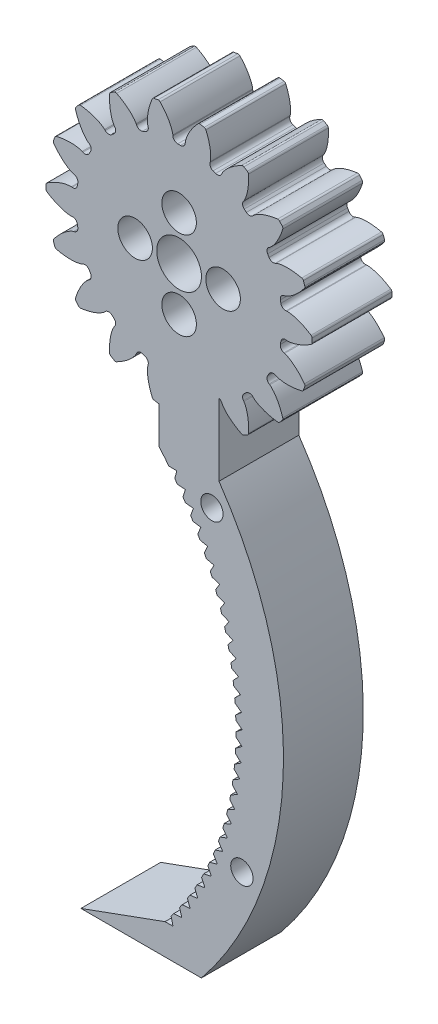
SolidWorks part; units mm, degrees
material "Alloy Steel"
ref_plane "Front" through (0, 0, 0) normal (0, 0, 1) x (1, 0, 0)
ref_plane "Top" through (0, 0, 0) normal (0, 1, 0) x (1, 0, 0)
ref_plane "Right" through (0, 0, 0) normal (1, 0, 0) x (0, 0, -1)
sketch "Sketch1" plane through (0, 0, 0) normal (0, 0, 1) x (1, 0, 0)
  circle A0 centre (0, 0) radius 21.1667
extrude "Boss-Extrude1" add sketch "Sketch1" along normal blind 12.7
sketch "Sketch3" plane through (0, 0, 0) normal (0, 0, 1) x (1, 0, 0)
  line L0 (0, 0) -> (43.7181, 0) construction
  line L2 (0, 0) -> (-0.9393, 16.3773) construction
  line L3 (0, 0) -> (0.9393, 16.3773) construction
  line L4 (0.9393, 16.3773) -> (0.9886, 17.2368) construction
  line L5 (0, 0) -> (0, 61.276) construction
  line L6 (-0.9393, 16.3773) -> (-0.9886, 17.2368) construction
  circle A0 centre (0, 0) radius 21.1667 construction
  circle A1 centre (0, 0) radius 19.05 construction
  circle A2 centre (0, 0) radius 17.2652 construction
  arc A3 (0.9393, 16.3773) -> (-0.9393, 16.3773) centre (0, 0) ccw construction
  arc A5 (3.1554, 20.9302) -> (-3.1554, 20.9302) centre (0, 0) ccw
  spline S0 degree 4 poles (-0.9886, 17.2368) (-0.9891, 17.2432) (-0.9907, 17.2612) (-0.9949, 17.295) (-1.0034, 17.35) (-1.0167, 17.4198) (-1.0366, 17.5096) (-1.0637, 17.6148) (-1.0972, 17.7297) (-1.1377, 17.8539) (-1.1816, 17.977) (-1.2287, 18.099) (-1.2785, 18.2198) (-1.3423, 18.3651) (-1.4236, 18.5381) (-1.5256, 18.738) (-1.6493, 18.9622) (-1.784, 19.1875) (-1.9235, 19.4067) (-2.0724, 19.6249) (-2.2221, 19.8338) (-2.3856, 20.0472) (-2.5406, 20.2425) (-2.7229, 20.4571) (-2.8726, 20.6291) (-3.0791, 20.8514) (-3.2038, 20.9813) (-3.3529, 21.1316) (-3.4207, 21.1975) (-3.4624, 21.2381) knots 0 0 0 0 0 0.005377 0.015084 0.028532 0.04661 0.064855 0.092111 0.119476 0.146842 0.174209 0.201575 0.228941 0.256307 0.307035 0.361767 0.4165 0.471232 0.525964 0.580697 0.635429 0.690161 0.744894 0.799626 0.854358 0.909091 0.954545 1 1 1 1 1 construction
  spline S1 degree 4 poles (-0.9886, 17.2368) (-0.9891, 17.2432) (-0.9907, 17.2612) (-0.9949, 17.295) (-1.0034, 17.35) (-1.0167, 17.4198) (-1.0366, 17.5096) (-1.0637, 17.6148) (-1.0972, 17.7297) (-1.1377, 17.8539) (-1.1816, 17.977) (-1.2287, 18.099) (-1.2785, 18.2198) (-1.3423, 18.3651) (-1.4236, 18.5381) (-1.5256, 18.738) (-1.6493, 18.9622) (-1.784, 19.1875) (-1.9235, 19.4067) (-2.0724, 19.6249) (-2.2221, 19.8338) (-2.3856, 20.0472) (-2.5406, 20.2425) (-2.7229, 20.4571) (-2.8726, 20.6291) (-3.0344, 20.8032) (-3.1141, 20.8874) (-3.1554, 20.9302) knots 0 0 0 0 0 0.005377 0.015084 0.028532 0.04661 0.064855 0.092111 0.119476 0.146842 0.174209 0.201575 0.228941 0.256307 0.307035 0.361767 0.4165 0.471232 0.525964 0.580697 0.635429 0.690161 0.744894 0.799626 0.854358 0.909091 0.909091 0.909091 0.909091 0.909091
  spline S2 degree 4 poles (0.9886, 17.2368) (0.9891, 17.2432) (0.9907, 17.2612) (0.9949, 17.295) (1.0034, 17.35) (1.0167, 17.4198) (1.0366, 17.5096) (1.0637, 17.6148) (1.0972, 17.7297) (1.1377, 17.8539) (1.1816, 17.977) (1.2287, 18.099) (1.2785, 18.2198) (1.3423, 18.3651) (1.4236, 18.5381) (1.5256, 18.738) (1.6493, 18.9622) (1.784, 19.1875) (1.9235, 19.4067) (2.0724, 19.6249) (2.2221, 19.8338) (2.3856, 20.0472) (2.5406, 20.2425) (2.7229, 20.4571) (2.8726, 20.6291) (3.0791, 20.8514) (3.2038, 20.9813) (3.3529, 21.1316) (3.4207, 21.1975) (3.4624, 21.2381) knots 0 0 0 0 0 0.005377 0.015084 0.028532 0.04661 0.064855 0.092111 0.119476 0.146842 0.174209 0.201575 0.228941 0.256307 0.307035 0.361767 0.4165 0.471232 0.525964 0.580697 0.635429 0.690161 0.744894 0.799626 0.854358 0.909091 0.954545 1 1 1 1 1 construction
  spline S3 degree 4 poles (0.9886, 17.2368) (0.9891, 17.2432) (0.9907, 17.2612) (0.9949, 17.295) (1.0034, 17.35) (1.0167, 17.4198) (1.0366, 17.5096) (1.0637, 17.6148) (1.0972, 17.7297) (1.1377, 17.8539) (1.1816, 17.977) (1.2287, 18.099) (1.2785, 18.2198) (1.3423, 18.3651) (1.4236, 18.5381) (1.5256, 18.738) (1.6493, 18.9622) (1.784, 19.1875) (1.9235, 19.4067) (2.0724, 19.6249) (2.2221, 19.8338) (2.3856, 20.0472) (2.5406, 20.2425) (2.7229, 20.4571) (2.8726, 20.6291) (3.0344, 20.8032) (3.1141, 20.8874) (3.1554, 20.9302) knots 0 0 0 0 0 0.005377 0.015084 0.028532 0.04661 0.064855 0.092111 0.119476 0.146842 0.174209 0.201575 0.228941 0.256307 0.307035 0.361767 0.4165 0.471232 0.525964 0.580697 0.635429 0.690161 0.744894 0.799626 0.854358 0.909091 0.909091 0.909091 0.909091 0.909091
  point P0 (0, 16.4042)
sketch "DCLTBC" plane through (0, 0, 0) normal (0, 0, 1) x (1, 0, 0)
  line L0 (0, 0) -> (41.04, 0) construction
  line L1 (-0.9393, 16.3773) -> (-0.9886, 17.2368) construction
  line L2 (0.9393, 16.3773) -> (0.9886, 17.2368) construction
  line L3 (-0.9393, 16.3773) -> (-0.9886, 17.2368)
  line L4 (0.9393, 16.3773) -> (0.9886, 17.2368)
  line L5 (0, 0) -> (0, 104.9356) construction
  circle A0 centre (0, 0) radius 21.1667
  circle A1 centre (0, 0) radius 19.05 construction
  circle A2 centre (0, 0) radius 17.2652 construction
  arc A3 (0.9393, 16.3773) -> (-0.9393, 16.3773) centre (0, 0) ccw construction
  arc A4 (0.9393, 16.3773) -> (-0.9393, 16.3773) centre (0, 0) ccw
  spline S0 degree 4 poles (-998.2859, -55.9585) (-15.2714, 14.5763) (-1.1564, 16.0258) (-0.9033, 16.703) (-1.0034, 17.35) (-1.0167, 17.4198) (-1.0366, 17.5096) (-1.0637, 17.6148) (-1.0972, 17.7297) (-1.1377, 17.8539) (-1.1816, 17.977) (-1.2287, 18.099) (-1.2785, 18.2198) (-1.3423, 18.3651) (-1.4236, 18.5381) (-1.5256, 18.738) (-1.6493, 18.9622) (-1.784, 19.1875) (-1.9235, 19.4067) (-2.0724, 19.6249) (-2.2221, 19.8338) (-2.3856, 20.0472) (-2.5406, 20.2425) (-2.7229, 20.4571) (-3.4042, 21.2399) (-5.6764, 23.4628) (17.3745, -0.7418) (-697.1444, 740.8893) knots -0.501613 -0.501613 -0.501613 -0.501613 -0.501613 0.005377 0.015084 0.028532 0.04661 0.064855 0.092111 0.119476 0.146842 0.174209 0.201575 0.228941 0.256307 0.307035 0.361767 0.4165 0.471232 0.525964 0.580697 0.635429 0.690161 0.744894 0.799626 0.854358 1.68661 1.68661 1.68661 1.68661 1.68661 only from (-0.9886, 17.2368) to (-3.1554, 20.9302) construction
  spline S1 degree 4 poles (998.2859, -55.9585) (15.2714, 14.5763) (1.1564, 16.0258) (0.9033, 16.703) (1.0034, 17.35) (1.0167, 17.4198) (1.0366, 17.5096) (1.0637, 17.6148) (1.0972, 17.7297) (1.1377, 17.8539) (1.1816, 17.977) (1.2287, 18.099) (1.2785, 18.2198) (1.3423, 18.3651) (1.4236, 18.5381) (1.5256, 18.738) (1.6493, 18.9622) (1.784, 19.1875) (1.9235, 19.4067) (2.0724, 19.6249) (2.2221, 19.8338) (2.3856, 20.0472) (2.5406, 20.2425) (2.7229, 20.4571) (3.4042, 21.2399) (5.6764, 23.4628) (-17.3745, -0.7418) (697.1444, 740.8893) knots -0.501613 -0.501613 -0.501613 -0.501613 -0.501613 0.005377 0.015084 0.028532 0.04661 0.064855 0.092111 0.119476 0.146842 0.174209 0.201575 0.228941 0.256307 0.307035 0.361767 0.4165 0.471232 0.525964 0.580697 0.635429 0.690161 0.744894 0.799626 0.854358 1.68661 1.68661 1.68661 1.68661 1.68661 only from (0.9886, 17.2368) to (3.1554, 20.9302) construction
  spline S2 degree 4 poles (-0.9886, 17.2368) (-0.9891, 17.2432) (-0.9907, 17.2612) (-0.9949, 17.295) (-1.0034, 17.35) (-1.0167, 17.4198) (-1.0366, 17.5096) (-1.0637, 17.6148) (-1.0972, 17.7297) (-1.1377, 17.8539) (-1.1816, 17.977) (-1.2287, 18.099) (-1.2785, 18.2198) (-1.3423, 18.3651) (-1.4236, 18.5381) (-1.5256, 18.738) (-1.6493, 18.9622) (-1.784, 19.1875) (-1.9235, 19.4067) (-2.0724, 19.6249) (-2.2221, 19.8338) (-2.3856, 20.0472) (-2.5406, 20.2425) (-2.7229, 20.4571) (-2.8726, 20.6291) (-3.0344, 20.8032) (-3.1141, 20.8874) (-3.1554, 20.9302) knots 0 0 0 0 0 0.005377 0.015084 0.028532 0.04661 0.064855 0.092111 0.119476 0.146842 0.174209 0.201575 0.228941 0.256307 0.307035 0.361767 0.4165 0.471232 0.525964 0.580697 0.635429 0.690161 0.744894 0.799626 0.854358 0.909091 0.909091 0.909091 0.909091 0.909091
  spline S3 degree 4 poles (0.9886, 17.2368) (0.9891, 17.2432) (0.9907, 17.2612) (0.9949, 17.295) (1.0034, 17.35) (1.0167, 17.4198) (1.0366, 17.5096) (1.0637, 17.6148) (1.0972, 17.7297) (1.1377, 17.8539) (1.1816, 17.977) (1.2287, 18.099) (1.2785, 18.2198) (1.3423, 18.3651) (1.4236, 18.5381) (1.5256, 18.738) (1.6493, 18.9622) (1.784, 19.1875) (1.9235, 19.4067) (2.0724, 19.6249) (2.2221, 19.8338) (2.3856, 20.0472) (2.5406, 20.2425) (2.7229, 20.4571) (2.8726, 20.6291) (3.0344, 20.8032) (3.1141, 20.8874) (3.1554, 20.9302) knots 0 0 0 0 0 0.005377 0.015084 0.028532 0.04661 0.064855 0.092111 0.119476 0.146842 0.174209 0.201575 0.228941 0.256307 0.307035 0.361767 0.4165 0.471232 0.525964 0.580697 0.635429 0.690161 0.744894 0.799626 0.854358 0.909091 0.909091 0.909091 0.909091 0.909091
extrude "Cut-Extrude-DCLTBC" cut sketch "DCLTBC" along normal through all
fillet "Fillet-Tip-DCLTBC" radius 0.3764 2 edges at (3.1554, 20.9302, 6.35) (-3.1554, 20.9302, 6.35)
fillet "Fillet-Root-DCLTBC" radius 0.7528 2 edges at (-0.9393, 16.3773, 6.35) (0.9393, 16.3773, 6.35)
pattern_circular "CirPattern-DCLTBC" count 18 over 360 about axis through (0, 0, 12.7) along (0, 0, 1) of "Cut-Extrude-DCLTBC", "Fillet-Tip-DCLTBC", "Fillet-Root-DCLTBC"
sketch "DCGTBC" [suppressed] plane through (0, 0, 0) normal (0, 0, 1) x (1, 0, 0)
  line L0 (0, 0) -> (41.04, 0) construction
  line L1 (-22.6634, 1.9828) -> (0, 0) construction
  line L2 (0, 0) -> (22.6634, 1.9828) construction
  line L3 (0, 0) -> (-16.5124, 0)
  line L5 (0, 0) -> (0, 104.9356) construction
  circle A0 centre (0, 0) radius 25
  circle A1 centre (0, 0) radius 24 construction
  circle A2 centre (0, 0) radius 21.7514 construction
  arc A3 (0.0626, 22.7499) -> (-0.0626, 22.7499) centre (0, 0) ccw construction
  arc A11 (22.6634, 1.9828) -> (-22.6634, 1.9828) centre (0, 0) ccw
  spline S4 degree 4 poles (999.7589, -2.0808) (12.8658, 20.0937) (0.2547, 20.6746) (0.0189, 21.2606) (0.0654, 21.8429) (0.0715, 21.8997) (0.0812, 21.973) (0.095, 22.0592) (0.1126, 22.1539) (0.1343, 22.2566) (0.1583, 22.3589) (0.1845, 22.4607) (0.2124, 22.562) (0.2486, 22.6844) (0.2952, 22.8308) (0.3543, 23.0013) (0.4268, 23.1939) (0.5065, 23.3893) (0.5897, 23.5809) (0.6793, 23.7735) (0.7698, 23.9592) (0.8695, 24.151) (0.9643, 24.3275) (1.0767, 24.524) (1.517, 25.277) (3.0654, 27.5692) (-13.787, 0.9944) (540.7091, 867.0187) knots -0.561807 -0.561807 -0.561807 -0.561807 -0.561807 0.005377 0.015084 0.028532 0.04661 0.064855 0.092111 0.119476 0.146842 0.174209 0.201575 0.228941 0.256307 0.307035 0.361767 0.4165 0.471232 0.525964 0.580697 0.635429 0.690161 0.744894 0.799626 0.854358 1.731906 1.731906 1.731906 1.731906 1.731906 only from (0.0598, 21.7513) to (1.3455, 24.9638) construction
  spline S5 degree 4 poles (-999.7589, -2.0808) (-12.8658, 20.0937) (-0.2547, 20.6746) (-0.0189, 21.2606) (-0.0654, 21.8429) (-0.0715, 21.8997) (-0.0812, 21.973) (-0.095, 22.0592) (-0.1126, 22.1539) (-0.1343, 22.2566) (-0.1583, 22.3589) (-0.1845, 22.4607) (-0.2124, 22.562) (-0.2486, 22.6844) (-0.2952, 22.8308) (-0.3543, 23.0013) (-0.4268, 23.1939) (-0.5065, 23.3893) (-0.5897, 23.5809) (-0.6793, 23.7735) (-0.7698, 23.9592) (-0.8695, 24.151) (-0.9643, 24.3275) (-1.0767, 24.524) (-1.517, 25.277) (-3.0654, 27.5692) (13.787, 0.9944) (-540.7091, 867.0187) knots -0.561807 -0.561807 -0.561807 -0.561807 -0.561807 0.005377 0.015084 0.028532 0.04661 0.064855 0.092111 0.119476 0.146842 0.174209 0.201575 0.228941 0.256307 0.307035 0.361767 0.4165 0.471232 0.525964 0.580697 0.635429 0.690161 0.744894 0.799626 0.854358 1.731906 1.731906 1.731906 1.731906 1.731906 only from (-0.0598, 21.7513) to (-1.3455, 24.9638) construction
  spline S6 degree 4 poles (0.0598, 21.7513) (0.0599, 21.7565) (0.0603, 21.7709) (0.0618, 21.7983) (0.0654, 21.8429) (0.0715, 21.8997) (0.0812, 21.973) (0.095, 22.0592) (0.1126, 22.1539) (0.1343, 22.2566) (0.1583, 22.3589) (0.1845, 22.4607) (0.2124, 22.562) (0.2486, 22.6844) (0.2952, 22.8308) (0.3543, 23.0013) (0.4268, 23.1939) (0.5065, 23.3893) (0.5897, 23.5809) (0.6793, 23.7735) (0.7698, 23.9592) (0.8695, 24.151) (0.9643, 24.3275) (1.0767, 24.524) (1.1693, 24.6823) (1.27, 24.8447) (1.3197, 24.9235) (1.3455, 24.9638) knots 0 0 0 0 0 0.005377 0.015084 0.028532 0.04661 0.064855 0.092111 0.119476 0.146842 0.174209 0.201575 0.228941 0.256307 0.307035 0.361767 0.4165 0.471232 0.525964 0.580697 0.635429 0.690161 0.744894 0.799626 0.854358 0.909091 0.909091 0.909091 0.909091 0.909091
  spline S7 degree 4 poles (-0.0598, 21.7513) (-0.0599, 21.7565) (-0.0603, 21.7709) (-0.0618, 21.7983) (-0.0654, 21.8429) (-0.0715, 21.8997) (-0.0812, 21.973) (-0.095, 22.0592) (-0.1126, 22.1539) (-0.1343, 22.2566) (-0.1583, 22.3589) (-0.1845, 22.4607) (-0.2124, 22.562) (-0.2486, 22.6844) (-0.2952, 22.8308) (-0.3543, 23.0013) (-0.4268, 23.1939) (-0.5065, 23.3893) (-0.5897, 23.5809) (-0.6793, 23.7735) (-0.7698, 23.9592) (-0.8695, 24.151) (-0.9643, 24.3275) (-1.0767, 24.524) (-1.1693, 24.6823) (-1.27, 24.8447) (-1.3197, 24.9235) (-1.3455, 24.9638) knots 0 0 0 0 0 0.005377 0.015084 0.028532 0.04661 0.064855 0.092111 0.119476 0.146842 0.174209 0.201575 0.228941 0.256307 0.307035 0.361767 0.4165 0.471232 0.525964 0.580697 0.635429 0.690161 0.744894 0.799626 0.854358 0.909091 0.909091 0.909091 0.909091 0.909091
  dimension "D1" = 5
  dimension "D2" = 5
extrude "Cut-Extrude-DCGTBC" [suppressed] cut sketch "DCGTBC" along normal through all
fillet "Fillet-Tip-DCGTBC" [suppressed] radius 0.3764
pattern_circular "CirPattern-DCGTBC" [suppressed] count 18 over 360
sketch "Sketch4" plane through (0, 0, 12.7) normal (0, 0, 1) x (1, 0, 0)
  circle A1 centre (0, 0) radius 3.556
  dimension "D1" = 7.112
extrude "Cut-Extrude2" cut sketch "Sketch4" against normal through all
sketch "Sketch5" plane through (0, 0, 12.7) normal (0, 0, 1) x (1, 0, 0)
  circle A0 centre (-7, 0) radius 1
  circle A1 centre (0, 7) radius 1
  circle A2 centre (7, 0) radius 1
  circle A3 centre (0, -7) radius 1
  point P12 (0, 0)
  dimension "D2" = 2
  dimension "D1" = 7
  dimension "D3" = 4
extrude "Cut-Extrude3" cut sketch "Sketch5" against normal through all
sketch "Sketch7" plane through (0, 0, 12.7) normal (0, 0, 1) x (1, 0, 0)
  line L0 (6.35, -14.1137) -> (6.35, -26.8137)
  line L2 (-3.175, -26.8137) -> (-3.175, -14.1137)
  line L3 (-3.175, -14.1137) -> (6.35, -14.1137)
  line L4 (-2.2365, -91.7884) -> (-15.6293, -96.6637)
  line L5 (-15.6293, -96.6637) -> (3.5477, -96.6637)
  arc A0 (-3.175, -26.8137) -> (-2.2365, -91.7884) centre (-41.7528, -59.8651) cw
  arc A1 (6.35, -26.8137) -> (3.5477, -96.6637) centre (-41.7528, -59.8651) cw
  dimension "D3" = 50.8
  dimension "D1" = 9.525
  dimension "D2" = 12.7
  dimension "D4" = 82.55
  dimension "D5" = 3.175
  dimension "D6" = 77.6747
  dimension "D7" = 19.177
extrude "Boss-Extrude3" add sketch "Sketch7" against normal through all
sketch "Sketch9" plane through (0, 0, 12.7) normal (0, 0, 1) x (1, 0, 0)
  circle A0 centre (5.2228, -31.0331) radius 1.778
  arc A1 (3.5477, -96.6637) -> (6.35, -26.8137) centre (-41.7528, -59.8651) ccw construction
  circle A2 centre (9.9936, -78.8467) radius 1.778
  arc A3 (-2.2365, -91.7884) -> (-3.175, -26.8137) centre (-41.7528, -59.8651) ccw construction
  dimension "D1" = 3.556
  dimension "D2" = 55.118
  dimension "D3" = 3.556
  dimension "D4" = 55.118
extrude "Cut-Extrude4" cut sketch "Sketch9" against normal blind 101.6
sketch "Sketch10" plane through (0, 0, 12.7) normal (0, 0, 1) x (1, 0, 0)
  circle A0 centre (-7, 0) radius 2.75
  circle A1 centre (0, -7) radius 2.75
  circle A2 centre (7, 0) radius 2.75
  circle A3 centre (0, 7) radius 2.75
  dimension "D1" = 5.5
extrude "Cut-Extrude5" cut sketch "Sketch10" against normal blind 7.7
sketch "Sketch11" plane through (0, 0, 12.7) normal (0, 0, 1) x (1, 0, 0)
  line L0 (-2.2365, -91.7884) -> (-0.9665, -91.7884)
  line L1 (-0.9665, -91.7884) -> (-1.2716, -90.5556)
  arc A0 (-2.2365, -91.7884) -> (-3.175, -26.8137) centre (-41.7528, -59.8651) ccw construction
  arc A1 (-2.2365, -91.7884) -> (-1.2716, -90.5556) centre (-41.7528, -59.8651) ccw
  dimension "D1" = 1.27
  dimension "D2" = 1.27
extrude "Cut-Extrude6" cut sketch "Sketch11" against normal through all
pattern_circular "CirPattern1" count 30 over 75 about axis through (-41.7528, -59.8651, 0) along (0, 0, 1) of "Cut-Extrude6"
equation "\"DiametralPitch\"= 12'Diametral Pitch"
equation "\"NumTeeth\"= 18'Number of Teeth"
equation "\"PressureAngle\"= 25deg'Pressure Angle"
equation "\"Addendum\"= 1 / \"DiametralPitch\"'Addendum"
equation "\"Dedendum\"= 1.25 / \"DiametralPitch\"'Dedendum"
equation "\"WorkingDepth\"= 2 / \"DiametralPitch\"'Working Depth - here for REF (Not used in building model)"
equation "\"WholeDepth\"= 2.25 / \"DiametralPitch\"'Whole Depth - here for REF (Not used in building model)"
equation "\"Clearance\"= .25 / \"DiametralPitch\"'Clearance"
equation "\"CircularPitch\"= pi / \"DiametralPitch\"'Circular Pitch - here for REF (Not used in building model)"
equation "\"PitchCircle\"= \"NumTeeth\" / \"DiametralPitch\"'Pitch Circle - or - Pitch Diameter"
equation "\"OutsideDiameter\"= ( \"NumTeeth\" + 2 ) / \"DiametralPitch\"'Outside Diameter"
equation "\"Fillet_Root\"= \"Clearance\" * cos ( \"PressureAngle\" ) * tan ( ( 90 + \"PressureAngle\" ) / 2 ) 'Fillet Root"
equation "\"AddendumCircle\"= \"PitchCircle\" + ( 2 * \"Addendum\" )'Addendum Circle - or - Addendum Diameter"
equation "\"DedendumCircle\"= \"PitchCircle\" - ( 2 * \"Dedendum\" )'Dedendum Circle - or - Dedendum Diameter"
equation "\"BaseCircle\"= \"PitchCircle\" * cos ( \"PressureAngle\" )'Base Circle - Base Diameter"
equation "\"PitchAngle\"= 360deg / \"NumTeeth\"'Pitch Angle"
equation "\"Alpha\"= sqr ( \"PitchCircle\" ^ 2 - \"BaseCircle\" ^ 2 ) / \"BaseCircle\" * 180 / PI - \"PressureAngle\"'Alpha - Used for Calculating Beta"
equation "\"Beta\"= ( \"PitchAngle\" / 4 - ( \"Alpha\" - 90 ) )'Beta - Used in definition of the parameters for the parametric equation driven curve"
equation "\"Gamma\"= ( \"PitchAngle\" / 4 - ( \"Alpha\" + 90 ) )'Gamma - Used in definition of the parameters for the parametric equation driven curve"
equation "\"Phi\"= sqr ( ( \"AddendumCircle\" / 2 ) ^ 2 - ( \"BaseCircle\" / 2 ) ^ 2 ) / ( \"BaseCircle\" / 2 )'Phi - Used in definition of the parameters for the parametric equation driven curve"
equation "\"DCGTBC\"= iif ( \"DedendumCircle\" > \"BaseCircle\" , \"unsuppressed\" , \"suppressed\" )'if Dedendum Circle IS GREATER THAN BaseCircle THEN UnsuppressORSuppress FEATURE"
equation "\"DCLTBC\"= iif ( \"DedendumCircle\" - .002 > \"BaseCircle\" , \"suppressed\" , \"unsuppressed\" )'if Dedendum Circle - .002 IS GREATER THAN BaseCircle THEN SuppressORUnsuppress FEATURE"
equation "\"Cut-Extrude-DCGTBC\"= iif ( \"DedendumCircle\" > \"BaseCircle\" , \"unsuppressed\" , \"suppressed\" )'if Dedendum Circle IS GREATER THAN BaseCircle THEN UnsuppressORSuppress FEATURE"
equation "\"Cut-Extrude-DCLTBC\"= iif ( \"DedendumCircle\" - .002 > \"BaseCircle\" , \"suppressed\" , \"unsuppressed\" )'if Dedendum Circle - .002 IS GREATER THAN BaseCircle THEN SuppressORUnsuppress FEATURE"
equation "\"CirPattern-DCGTBC\"= iif ( \"DedendumCircle\" > \"BaseCircle\" , \"unsuppressed\" , \"suppressed\" )'if Dedendum Circle IS GREATER THAN BaseCircle THEN UnsuppressORSuppress FEATURE"
equation "\"CirPattern-DCLTBC\"= iif ( \"DedendumCircle\" - .002 > \"BaseCircle\" , \"suppressed\" , \"unsuppressed\" )'if Dedendum Circle - .002 IS GREATER THAN BaseCircle THEN SuppressORUnsuppress FEATURE"
equation "\"Fillet-Tip-DCGTBC\"= iif ( \"DedendumCircle\" > \"BaseCircle\" , \"unsuppressed\" , \"suppressed\" )'if Dedendum Circle IS GREATER THAN BaseCircle THEN UnsuppressORSuppress FEATURE"
equation "\"Fillet-Tip-DCLTBC\"= iif ( \"DedendumCircle\" - .002 > \"BaseCircle\" , \"suppressed\" , \"unsuppressed\" )'if Dedendum Circle - .002 IS GREATER THAN BaseCircle THEN SuppressORUnsuppress FEATURE"
equation "\"Fillet-Root-DCLTBC\"= iif ( \"DedendumCircle\" - .002 > \"BaseCircle\" , \"suppressed\" , \"unsuppressed\" )'if Dedendum Circle - .002 IS GREATER THAN BaseCircle THEN SuppressORUnsuppress FEATURE"
equation "\"D1@CirPattern-DCGTBC\"= \"NumTeeth\"'Number of Teeth"
equation "\"D1@CirPattern-DCLTBC\"= \"NumTeeth\"'Number of Teeth"
equation "\"D1@Fillet-Tip-DCGTBC\"= \"Fillet_Root\" / 2 'Tip Rad For Large No of Teeth"
equation "\"D1@Fillet-Tip-DCLTBC\"=\"Fillet_Root\" / 2'Tip Rad For Small No of Teeth"
equation "\"D1@Fillet-Root-DCLTBC\"= \"Fillet_Root\"'Fillet Root"
